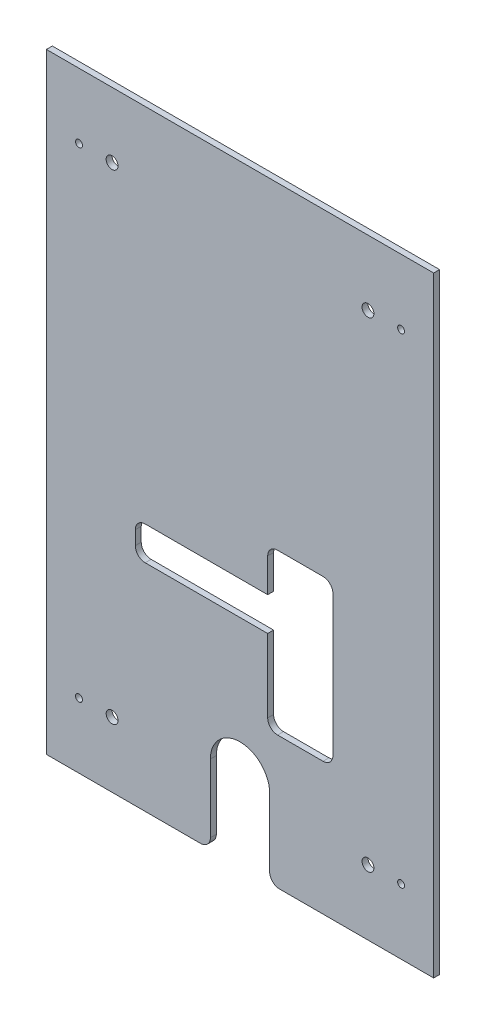
SolidWorks part; units mm, degrees
ref_plane "Plan de face" through (0, 0, 0) normal (0, 0, 1) x (1, 0, 0)
ref_plane "Plan de dessus" through (0, 0, 0) normal (0, 1, 0) x (1, 0, 0)
ref_plane "Plan de droite" through (0, 0, 0) normal (1, 0, 0) x (0, 0, -1)
sketch "Esquisse1" plane through (0, 0, 0) normal (0, 0, 1) x (1, 0, 0)
  line L0 (0, 154.5) -> (0, -154.5) construction
  line L1 (98, 154.5) -> (-98, 154.5)
  line L2 (98, 154.5) -> (98, -154.5)
  line L3 (98, -154.5) -> (-98, -154.5)
  line L4 (-98, 154.5) -> (-98, -154.5)
  line L5 (98, 154.5) -> (-98, -154.5) construction
  line L6 (98, -154.5) -> (-98, 154.5) construction
  line L7 (-98, 0) -> (98, 0) construction
  line L8 (81.5, 121.5) -> (64.75, 121.5) construction
  circle A0 centre (-81.5, 121.5) radius 1.75
  circle A1 centre (81.5, 121.5) radius 1.75
  circle A2 centre (81.5, -121.5) radius 1.75
  circle A3 centre (-81.5, -121.5) radius 1.75
  circle A4 centre (64.75, 121.5) radius 3
  circle A6 centre (-64.75, 121.5) radius 3
  circle A7 centre (-64.75, -121.5) radius 3
  circle A8 centre (64.75, -121.5) radius 3
  point P0 (0, 0)
  dimension "D2" = 3.5
  dimension "D7" = 6
  dimension "D1" = 163
  dimension "D3" = 309
  dimension "D4" = 196
  dimension "D5" = 33
  dimension "D6" = 16.75
extrude "Boss.-Extru.1" add sketch "Esquisse1" along normal blind 3
sketch "Esquisse2" plane through (0, 0, 3) normal (0, 0, 1) x (1, 0, 0)
  line L0 (0, -154.5) -> (0, -115) construction
  line L1 (-98, -154.5) -> (98, -154.5) construction
  line L2 (-15, -154.5) -> (-15, -115)
  line L3 (15, -154.5) -> (15, -115)
  arc A0 (-15, -154.5) -> (15, -154.5) centre (0, -154.5) ccw
  arc A1 (15, -115) -> (-15, -115) centre (0, -115) ccw
  point P5 (0, -134.75)
  dimension "D2" = 15
  dimension "D1" = 39.5
extrude "Enlèv. mat.-Extru.1" cut sketch "Esquisse2" against normal up to next
fillet "Congé1" radius 5 2 edges at (15, -154.5, 1.5) (-15, -154.5, 1.5)
sketch "Esquisse3" plane through (0, 0, 3) normal (0, 0, 1) x (1, 0, 0)
  line L0 (-98, -154.5) -> (-20, -154.5) construction
  line L1 (-53, -28.5) -> (14, -28.5)
  line L2 (-53, -28.5) -> (-53, -45.5)
  line L3 (-53, -45.5) -> (14, -45.5)
  line L4 (14, -28.5) -> (14, -45.5) construction
  line L6 (-98, 154.5) -> (-98, -154.5) construction
  line L7 (14, -6.5) -> (14, -28.5)
  line L8 (47, -6.5) -> (14, -6.5)
  line L9 (47, -6.5) -> (47, -87.5)
  line L10 (47, -87.5) -> (14, -87.5)
  line L11 (14, -6.5) -> (14, -87.5) construction
  line L12 (14, -45.5) -> (14, -87.5)
  dimension "D1" = 17
  dimension "D2" = 126
  dimension "D3" = 67
  dimension "D4" = 45
  dimension "D5" = 33
  dimension "D6" = 22
  dimension "D7" = 42
extrude "Enlèv. mat.-Extru.2" cut sketch "Esquisse3" against normal through all
fillet "Congé2" radius 5 6 edges at (-53, -45.5, 1.5) (-53, -28.5, 1.5) (14, -87.5, 1.5) (47, -87.5, 1.5) (47, -6.5, 1.5) (14, -6.5, 1.5)
